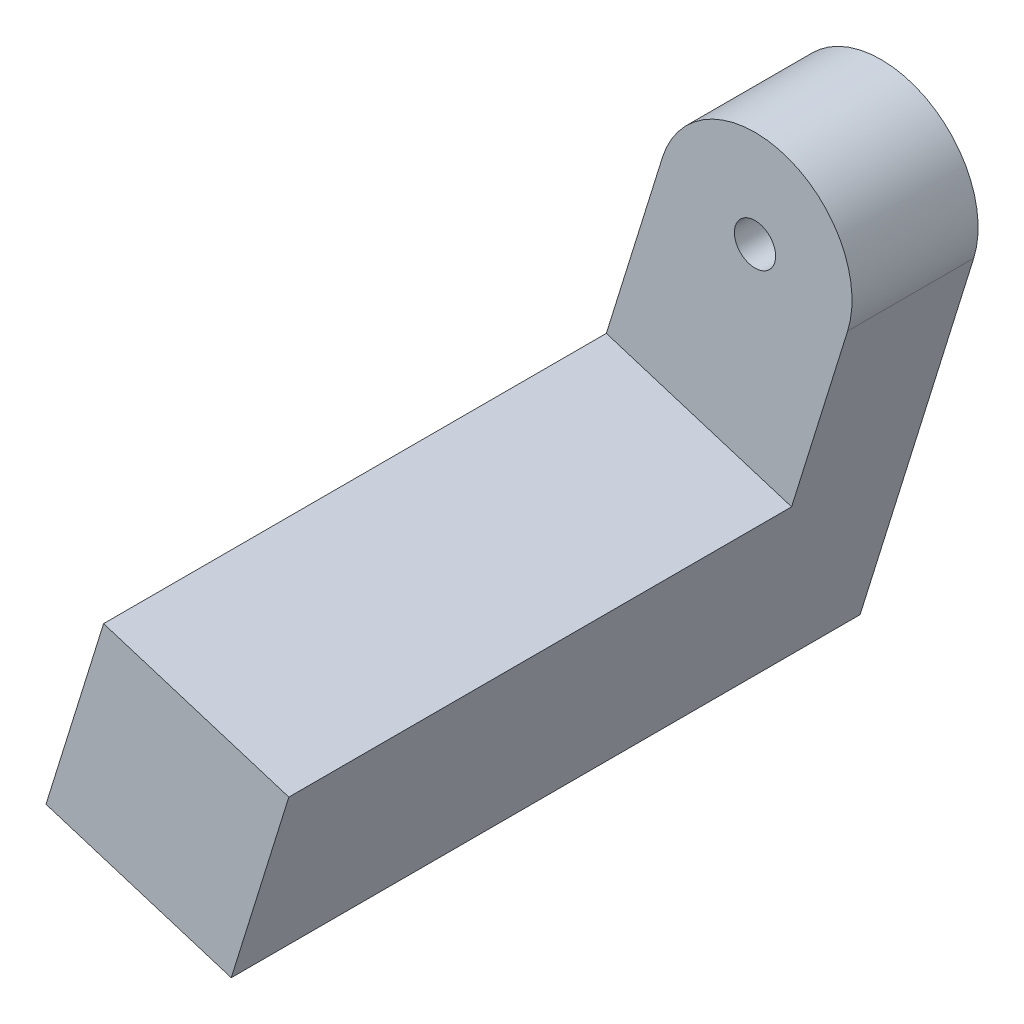
SolidWorks part; units mm, degrees
ref_plane "Front Plane" through (0, 0, 0) normal (0, 0, 1) x (1, 0, 0)
ref_plane "Top Plane" through (0, 0, 0) normal (0, 1, 0) x (1, 0, 0)
ref_plane "Right Plane" through (0, 0, 0) normal (1, 0, 0) x (0, 0, -1)
sketch "Sketch1" plane through (0, 0, 0) normal (0, 0, 1) x (1, 0, 0)
  circle A0 centre (0, 0) radius 2.3
  arc A1 (-2.3, 0) -> (2.3, 0) centre (0, 0) ccw construction
  circle A2 centre (0, 0) radius 4
  dimension "D1" = 8
extrude "Boss-Extrude1" add sketch "Sketch1" against normal up to surface (3.2 mm away)
sketch "Sketch2" plane through (0, 0, 0) normal (0, 0, 1) x (1, 0, 0)
  circle A0 centre (0, 0) radius 0.85
  circle A1 centre (0, 0) radius 4
extrude "Boss-Extrude2" add sketch "Sketch2" along normal blind 2
ref_plane "Plane1" through (3.8197, -1.1875, 0) normal (0.9549, -0.2969, 0) x (0, 0, -1)
sketch "Sketch5" plane through (3.8197, -1.1875, 0) normal (0.9549, -0.2969, 0) x (0, 0, -1)
  line L0 (-2, 0) -> (3.2, 0)
  line L1 (-2, 0) -> (-2, -7.7849)
  line L2 (3.2, 0) -> (3.2, -15.7849)
  line L4 (-2, 4) -> (-2, -4) construction
  line L5 (3.2, -4) -> (3.2, 4) construction
  line L6 (-22.7319, -7.7849) -> (-2, -7.7849)
  line L7 (-22.7319, -7.7849) -> (-22.7319, -15.7849)
  line L9 (-22.7319, -15.7849) -> (3.2, -15.7849)
  point P5 (0, 0)
  dimension "D1" = 8
extrude "Boss-Extrude3" add sketch "Sketch5" against normal blind 8
sketch "Sketch6" plane through (0, 0, 2) normal (0, 0, 1) x (1, 0, 0)
  circle A0 centre (0, 0) radius 0.85
  dimension "D1" = 1.7
extrude "Cut-Extrude1" cut sketch "Sketch6" against normal through all
